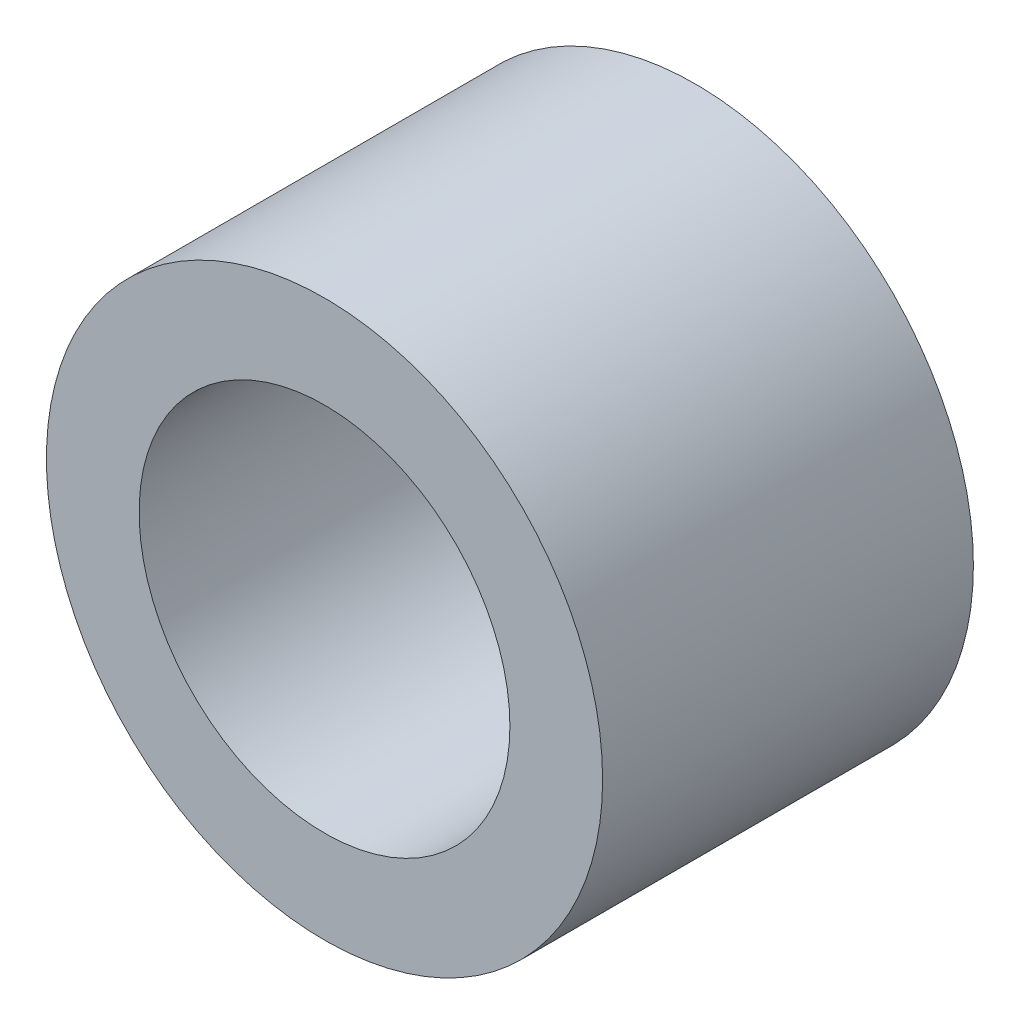
SolidWorks part; units mm, degrees
material "Aluminum Bronze"
ref_plane "Front Plane" through (0, 0, 0) normal (0, 0, 1) x (1, 0, 0)
ref_plane "Top Plane" through (0, 0, 0) normal (0, 1, 0) x (1, 0, 0)
ref_plane "Right Plane" through (0, 0, 0) normal (1, 0, 0) x (0, 0, -1)
sketch "Sketch1" plane through (0, 0, 0) normal (0, 0, 1) x (1, 0, 0)
  circle A0 centre (0, 0) radius 3.175
  circle A1 centre (0, 0) radius 4.7625
  dimension "D1" = 6.35
  dimension "D2" = 9.525
extrude "Boss-Extrude1" add sketch "Sketch1" along normal blind 6.35
